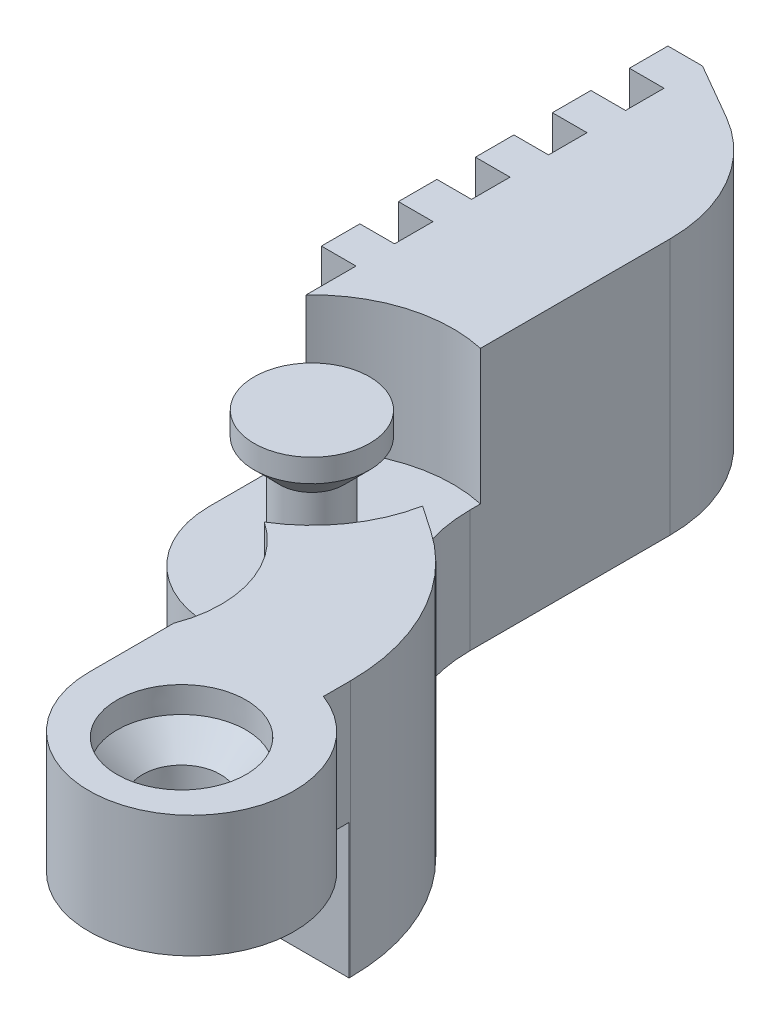
SolidWorks part; units mm, degrees
ref_plane "Front Plane" through (0, 0, 0) normal (0, 0, 1) x (1, 0, 0)
ref_plane "Top Plane" through (0, 0, 0) normal (0, 1, 0) x (1, 0, 0)
ref_plane "Right Plane" through (0, 0, 0) normal (1, 0, 0) x (0, 0, -1)
sketch "Sketch1" plane through (0, 0, 0) normal (0, 1, 0) x (1, 0, 0)
  line L1 (-17, -215.5724) -> (17, -215.5724) construction
  line L2 (-17, -215.5724) -> (-17, -189.1954) construction
  line L3 (1.6018, -189.1954) -> (-50.2392, -189.1954) construction
  line L5 (-2.423, -153.735) -> (-27.7, -153.735) construction
  line L6 (-20.5998, -153.2947) -> (-27.7, -149.1954) construction
  line L7 (-27.7, -149.1954) -> (-27.7, -179.735) construction
  line L8 (-14.5998, -163.687) -> (-14.5998, -179.2892)
  line L9 (-8, -208.9691) -> (-8, -215.5724)
  line L11 (-17, -197.1954) -> (65.6713, -197.1954) construction
  line L12 (-25, -153.7542) -> (-25, -156.7542)
  line L14 (-25, -150.7542) -> (-27.7, -150.7542)
  line L15 (-27.7, -150.7542) -> (-27.7, -153.7542)
  line L16 (-27.7, -153.7542) -> (-25, -153.7542)
  line L17 (-25, -156.7542) -> (-27.7, -156.7542)
  line L18 (-27.7, -156.7542) -> (-27.7, -159.7542)
  line L19 (-27.7, -159.7542) -> (-25, -159.7542)
  line L20 (-25, -162.7542) -> (-27.7, -162.7542)
  line L21 (-27.7, -162.7542) -> (-27.7, -165.7542)
  line L22 (-27.7, -165.7542) -> (-25, -165.7542)
  line L23 (-25, -168.7542) -> (-27.7, -168.7542)
  line L24 (-27.7, -168.7542) -> (-27.7, -171.7542)
  line L25 (-27.7, -171.7542) -> (-25, -171.7542)
  line L26 (-25, -174.7542) -> (-27.7, -174.7542)
  line L27 (-27.7, -174.7542) -> (-27.7, -177.7542)
  line L28 (-27.7, -177.7542) -> (-25, -177.7542)
  line L29 (-25, -159.7542) -> (-25, -162.7542)
  line L30 (-25, -165.7542) -> (-25, -168.7542)
  line L31 (-25, -171.7542) -> (-25, -174.7542)
  line L32 (-25, -177.7542) -> (-25, -189.1954)
  line L33 (-25, -150.7542) -> (-20.5998, -153.2947)
  line L34 (-9.3723, -189.1954) -> (-4.1974, -192.7334)
  line L35 (2.7726, -205.9416) -> (2.7726, -208.0682)
  arc A0 (-8, -215.5724) -> (8, -215.5724) centre (0, -215.5724) ccw
  arc A1 (-25, -189.1954) -> (-17, -197.1954) centre (-17, -189.1954) ccw
  arc A3 (-14.5998, -163.687) -> (-20.5998, -153.2947) centre (-26.5998, -163.687) ccw
  arc A4 (-14.5998, -179.2892) -> (-9.3723, -189.1954) centre (-2.5998, -179.2892) ccw
  arc A6 (-8, -215.5724) -> (2.7726, -208.0682) centre (0, -215.5724) ccw construction
  arc A7 (-8, -215.5724) -> (2.7726, -208.0682) centre (0, -215.5724) ccw
  arc A8 (-4.1974, -192.7334) -> (2.7726, -205.9416) centre (-13.2274, -205.9416) cw
  arc A9 (-17, -197.1954) -> (-8, -208.9691) centre (-16.1127, -205.8439) cw
  point P9 (1.6018, -189.1954)
  dimension "D2" = 16
  dimension "D4" = 16
  dimension "D6" = 16
  dimension "D7" = 2.7
  dimension "D8" = 30
  dimension "D9" = 3
  dimension "D3" = 34
  dimension "D11" = 40
  dimension "D10" = 5
extrude "Boss-Extrude1" add sketch "Sketch1" along normal blind 20
ref_plane "Plane1" through (0, 0, 0) normal (1, 0, 0) x (0, 0, -1)
sketch "Sketch2" plane through (0, 0, 0) normal (1, 0, 0) x (0, 0, -1)
  line L0 (-215.5724, 0) -> (-223.5724, 0) construction
  line L1 (-225.683, -0.5) -> (-206.0724, -0.5)
  line L2 (-225.683, -0.5) -> (-225.683, 10.5)
  line L3 (-225.683, 10.5) -> (-206.0724, 10.5)
  line L4 (-206.0724, -0.5) -> (-206.0724, 10.5)
  line L6 (-223.5724, 20) -> (-223.5724, 0) construction
  dimension "D2" = 0.5
  dimension "D1" = 10.5
  dimension "D3" = 17.5
extrude "Cut-Extrude1" cut sketch "Sketch2" against normal through all both and the other way through all
sketch "Sketch3" plane through (0, 0, 0) normal (1, 0, 0) x (0, 0, -1)
  line L2 (-215.5724, 3.9608) -> (-215.5724, 10)
  line L3 (-212.5724, 10) -> (-212.5724, 3.9608)
  line L4 (-212.5724, 3.9608) -> (-215.5724, 3.9608)
  line L5 (-212.5724, 10) -> (-212.5724, 16)
  line L6 (-212.5724, 16) -> (-210.5724, 18)
  line L7 (-210.5724, 18) -> (-210.5724, 20)
  line L8 (-210.5724, 20) -> (-215.5724, 20)
  line L9 (-215.5724, 10) -> (-215.5724, 20)
  line B0 (-212.5724, 10) -> (-207.5724, 10)
  line B1 (-213.0724, 10) -> (-213.0724, 16.2071)
  line B2 (-215.5724, 10) -> (-213.0724, 10)
  line B3 (-215.5724, 20) -> (-215.5724, 10)
  line B4 (-211.0724, 20) -> (-215.5724, 20)
  line B5 (-211.0724, 18.2071) -> (-211.0724, 20)
  line B6 (-213.0724, 16.2071) -> (-211.0724, 18.2071)
  line B7 (-207.5724, 10) -> (-207.5724, 20)
  line B8 (-212.5724, 16) -> (-212.5724, 10)
  line B9 (-210.5724, 18) -> (-212.5724, 16)
  line B10 (-210.5724, 20) -> (-210.5724, 18)
  line B11 (-207.5724, 20) -> (-210.5724, 20)
sketch_block_instance "Block3-1"
sketch_block "Block3"
sketch "Sketch4" plane through (0, 0, 0) normal (1, 0, 0) x (0, 0, -1)
  line L8 (-213.3718, 3.9994) -> (-216.3527, 4.0089)
  line L9 (-211.3152, 21.7444) -> (-216.3527, 21.7444)
  line L10 (-211.3272, 17.9839) -> (-211.3152, 21.7444)
  line L11 (-213.3336, 15.9903) -> (-211.3272, 17.9839)
  line L12 (-213.3527, 9.9904) -> (-213.3336, 15.9903)
  line L13 (-213.3527, 9.9904) -> (-213.3718, 3.9994)
  line L14 (-216.3527, 4.0089) -> (-216.3527, 9.9999)
  line L15 (-216.3527, 9.9999) -> (-216.3527, 21.7444)
  line L18 (-208.9691, 0) -> (-215.5724, 0) construction
  point P9 (-216.3527, 0)
revolve "Cut-Revolve8" cut sketch "Sketch4" angle 360 about L14
ref_plane "Plane2" through (0, 0, 189.1954) normal (0, 0, 1) x (1, 0, 0)
sketch "Sketch7" plane through (0, 20, 0) normal (0, 1, 0) x (1, 0, 0)
  circle A0 centre (-17, -189.1954) radius 8 construction
  circle A1 centre (-17, -189.1954) radius 11
  dimension "D1" = 3
extrude "Cut-Extrude2" cut sketch "Sketch7" against normal blind 10.5
sketch "Sketch6" plane through (0, 0, 189.1954) normal (0, 0, 1) x (1, 0, 0)
  line L0 (-17, 0) -> (-17, 20) construction
  line L2 (-14.5, 10) -> (-14.5, 3.0629)
  line L3 (-14.5, 3.0629) -> (-17, 3.0629)
  line L4 (-17, 3.0629) -> (-17, 10)
  line L5 (8, 20) -> (-8, 20) construction
  point P3 (-17, 10)
  line B0 (-14, 10) -> (-9, 10)
  line B1 (-14.5, 10) -> (-14.5, 16.2071)
  line B2 (-17, 10) -> (-14.5, 10)
  line B3 (-17, 20) -> (-17, 10)
  line B4 (-12.5, 20) -> (-17, 20)
  line B5 (-12.5, 18.2071) -> (-12.5, 20)
  line B6 (-14.5, 16.2071) -> (-12.5, 18.2071)
  line B7 (-9, 10) -> (-9, 20)
  line B8 (-14, 16) -> (-14, 10)
  line B9 (-12, 18) -> (-14, 16)
  line B10 (-12, 20) -> (-12, 18)
  line B11 (-9, 20) -> (-12, 20)
sketch_block_instance "Block3-2"
revolve "Revolve2" add sketch "Sketch6" angle 360 about L0
equation "\"pin_diameter\"= 5"
equation "\"pin_cap_diameter\"= 10"
equation "\"pin_chamfer\"=2"
equation "\"allowance1\"= 0.5"
equation "\"steep_angle\"= 45"
equation "\"pin_height\"=20"
equation "\"gen_diameter\"= 16"
equation "\"allowance2\"= 1.5"
equation "\"upper_height\" = 10"
equation "\"lower_height\"= 10"
equation "\"center_center_distance\"=29"
equation "\"gen_width\"=7"
equation "\"D2@Sketch1\"=\"gen_diameter\""
equation "\"D4@Sketch1\"=\"gen_diameter\""
equation "\"D1@Boss-Extrude1\"=\"pin_height\""
equation "\"D2@Sketch2\"=\"allowance1\""
equation "\"1\"= \"allowance1\""
